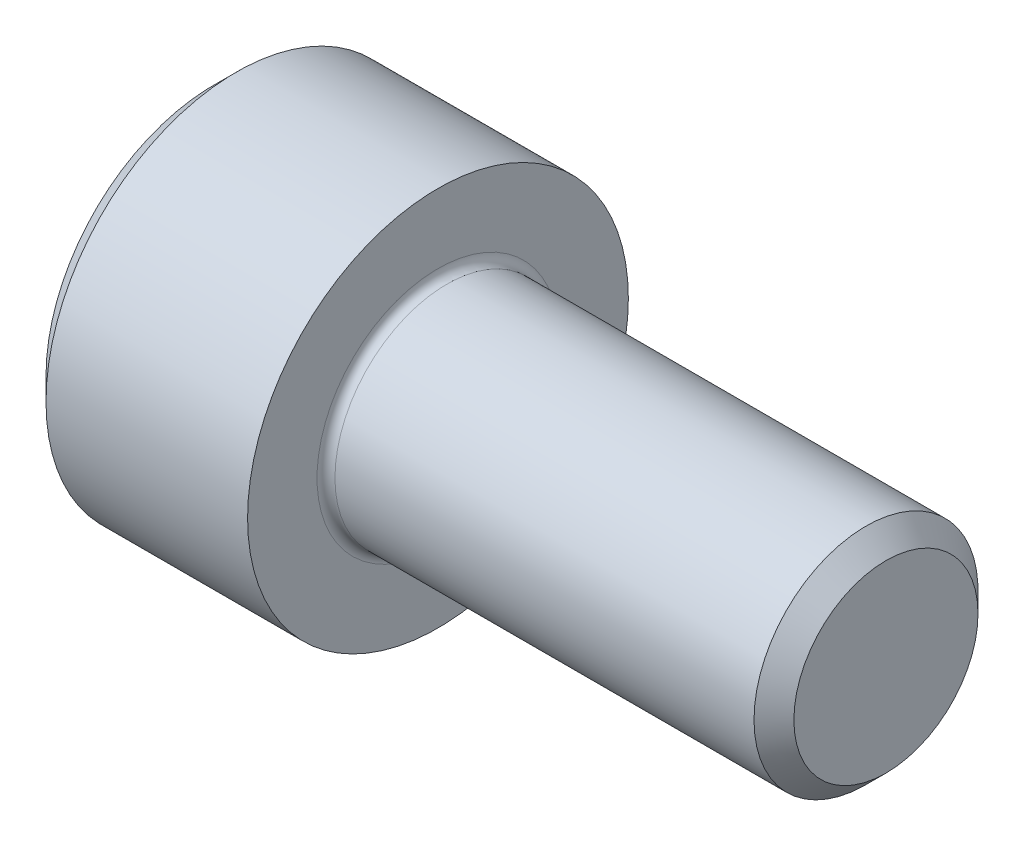
SolidWorks part; units mm, degrees
revolve "Base-Revolve" add sketch "BodySke"
sketch "BodySke" plane through (0, 0, 0) normal (0, 0, 1) x (1, 0, 0)
  line L0 (0, 0) -> (0, 3.75)
  line L1 (0.5, 4.25) -> (5, 4.25)
  line L2 (5, 4.25) -> (5, 2.5)
  line L3 (5, 2.5) -> (14.555, 2.5)
  line L4 (15, 2.055) -> (15, 0)
  line L5 (15, 0) -> (0, 0)
  line L6 (-31.75, 0) -> (127, 0) construction
  line L7 (0, 3.75) -> (0.5, 4.25)
  line L8 (15, 2.055) -> (14.555, 2.5)
  line L9 (0, -3.75) -> (0.5, -4.25) construction
  line L10 (15, -2.055) -> (14.555, -2.5) construction
  line L11 (5.8, 9.525) -> (5.8, 3.175) construction
  line L12 (5, 9.525) -> (5, 3.175) construction
  line L13 (-35, 9.525) -> (-35, 3.175) construction
  dimension "Diameter" = 5
  dimension "Head_ht" = 5
  dimension "Length" = 10
  dimension "Body_ch_ang" = 45
  dimension "Head_dia" = 8.5
  dimension "Head_ch_ang" = 45
  dimension "Minor_dia" = 4.11
  dimension "Advance" = 0.8
  dimension "Thread_nom" = 10
  dimension "Thread_length" = 50
  dimension "Head_ch_ht" = 0.5
cosmetic thread "ThreadCosmetic"
fillet "Fillet1" radius 0.2 1 edges at (5, 0, 2.5)
ref_plane "Plane1" through (0, 0, 0) normal (0, 0, 1) x (1, 0, 0)
ref_plane "Plane2" through (0, 0, 0) normal (0, 1, 0) x (1, 0, 0)
ref_plane "Plane3" through (0, 0, 0) normal (1, 0, 0) x (0, 0, -1)
sketch "Sketch2" plane through (0, 0, 0) normal (0, 0, 1) x (1, 0, 0)
  line L0 (0, 2.042) -> (2.5, 2.042)
  line L1 (2.5, 2.042) -> (3.6789, 0)
  line L2 (-31.75, 0) -> (127, 0) construction
  line L3 (3.6789, 0) -> (0, 0)
  line L4 (0, 0) -> (0, 2.042)
  line L5 (0, 3.75) -> (0, -3.75) construction
  line L6 (0, 0) -> (47.625, 0) construction
  line L7 (5, -4.25) -> (5, 4.25) construction
  dimension "D1" = 2.042
  dimension "D2" = 60
revolve "Hex-PreBroach" cut sketch "Sketch2" angle 360 about L6
sketch "Sketch3" plane through (0, 0, 0) normal (-1, 0, 0) x (0, 0.5, 0.866)
  line L0 (1.1789, 2.042) -> (-1.1789, 2.042)
  line L1 (-1.1789, 2.042) -> (-2.3579, 0)
  line L2 (1.1789, 2.042) -> (2.3579, 0)
  line L3 (1.1789, -2.042) -> (2.3579, 0)
  line L4 (1.1789, -2.042) -> (-1.1789, -2.042)
  line L5 (-1.1789, -2.042) -> (-2.3579, 0)
  dimension "D1" = 2.042
  dimension "D2" = 2.042
  dimension "Hex_size" = 4.084
extrude "Hex" cut sketch "Sketch3" against normal blind 2.5
sketch "Sketch4" plane through (0, 0, 0) normal (-1, 0, 0) x (0, 0, 1)
  line L0 (0, 0) -> (2.3876, 0)
  line L1 (0, 0) -> (6.1484, 3.5498) construction
  line L2 (0, 0) -> (1.1938, 2.0677)
  line L3 (1.9883, 0.576) -> (2.2704, 0.7389)
  line L4 (1.493, 1.4339) -> (1.7751, 1.5968)
  arc A0 (1.9883, 0.576) -> (1.493, 1.4339) centre (0, 0) ccw
  arc A1 (2.3876, 0) -> (2.2704, 0.7389) centre (0, 0) ccw
  arc A2 (1.1938, 2.0677) -> (1.7751, 1.5968) centre (0, 0) cw
  dimension "D1" = 30
  dimension "D2" = 60
  dimension "Spline_p_dim" = 0.9906
  dimension "D3" = 0.4953
extrude "Spline" [suppressed] cut sketch "Sketch4" against normal blind 2.5
pattern_circular "CirPattern1" [suppressed] count 6 every 60
sketch "Sketch5" plane through (0, 0, 0) normal (0, 0, 1) x (1, 0, 0)
  line L0 (-31.75, 0) -> (127, 0) construction
  line L2 (0, 3.75) -> (0, -3.75) construction
  circle A0 centre (2, 0) radius 0.675
  dimension "Drilled_hole_dia" = 1.35
  dimension "Drilled_hole_loc" = 2
extrude "Hole" [suppressed] cut sketch "Sketch5" against normal through all and the other way through all
pattern_circular "Drilled-4" [suppressed] count 2 every 60
pattern_circular "Drilled-6" [suppressed] count 3 every 60
sketch "ThdSchSke" plane through (0, 0, 0) normal (0, 0, 1) x (1, 0, 0)
  line L0 (5.8, -2.055) -> (5.4884, -2.5)
  line L1 (5.8, -2.055) -> (6.1116, -2.5)
  line L2 (6.1116, -2.5) -> (6.1116, -3.125)
  line L3 (-3.175, 0) -> (5.1513, 0) construction
  line L5 (6.1116, -3.125) -> (5.4884, -3.125)
  line L6 (5.4884, -3.125) -> (5.4884, -2.5)
  line L7 (0, 3.75) -> (0, -3.75) construction
  dimension "Thread_minor" = 4.11
  dimension "Diameter" = 5
  dimension "Start" = 5.8
revolve "ThreadSchematic" [suppressed] cut sketch "ThdSchSke" angle 360 about L3
pattern_linear "ThdSchPat" [suppressed]
equation "\"D2@Sketch3\" = \"Hex_size@Sketch3\" / 2"
equation "\"D1@Sketch3\" = \"Hex_size@Sketch3\" / 2"
equation "\"D1@Sketch2\" = \"Hex_size@Sketch3\" / 2"
equation "\"D3@Sketch4\" = \"Spline_p_dim@Sketch4\" / 2"
equation "\"Thread_minor@ThreadCosmetic\"  =  \"Minor_dia@BodySke\""
equation "\"D2@CirPattern1\" = 360 / \"Num_teeth@CirPattern1\""
equation "\"Wall_thickness@Sketch2\" = \"Head_ht@BodySke\" - \"Key_eng@Hex\""
equation "\"Thread_length@ThreadCosmetic\" = ((sgn( (\"Length@BodySke\" - \"Advance@BodySke\" ) - \"Thread_nom@BodySke\" )-1)*( (\"Length@BodySke\" - \"Advance@BodySke\" ) - \"Thread_nom@BodySke\" ))/-2+ \"Thread_nom@BodySke\""
equation "\"Thread_minor@ThdSchSke\" = \"Minor_dia@BodySke\""
equation "\"Diameter@ThdSchSke\" = \"Diameter@BodySke\""
equation "\"Overcut@ThdSchSke\" = \"Diameter@BodySke\" * 1.25"
equation "\"Start@ThdSchSke\" = \"Head_ht@BodySke\" + \"Length@BodySke\" - \"Thread_length@ThreadCosmetic\"  '---Non-countersunk---"
equation "\"Num_threads@ThdSchPat\" = int( \"Thread_length@ThreadCosmetic\" / \"Advance@BodySke\" + 0.999 )  + 1"
equation "\"Advance@ThdSchPat\" = \"Thread_length@ThreadCosmetic\" /  (\"Num_threads@ThdSchPat\" - 1) 'relax it"
equation "\"Num_threads@ThdSchPat\" = \"Num_threads@ThdSchPat\" - sgn( \"Num_threads@ThdSchPat\" - 1) '---chamfered tips only---"
